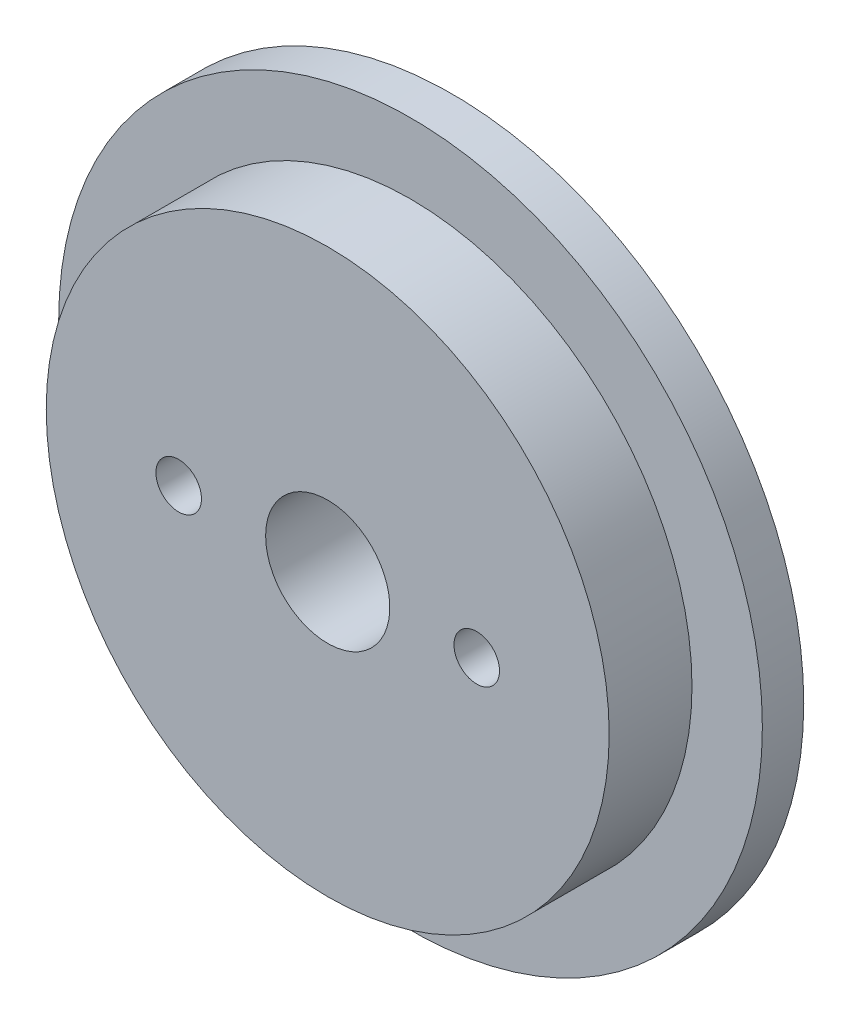
SolidWorks part; units mm, degrees
ref_plane "Ebene vorne" through (0, 0, 0) normal (0, 0, 1) x (1, 0, 0)
ref_plane "Ebene oben" through (0, 0, 0) normal (0, 1, 0) x (1, 0, 0)
ref_plane "Ebene rechts" through (0, 0, 0) normal (1, 0, 0) x (0, 0, -1)
sketch "Skizze1" plane through (0, 0, 0) normal (0, 0, 1) x (1, 0, 0)
  circle A0 centre (0, 0) radius 34
  dimension "D1" = 68
extrude "Aufsatz-Linear austragen1" add sketch "Skizze1" along normal blind 10 contours A0
sketch "Skizze3" plane through (0, 0, 0) normal (0, 0, -1) x (-1, 0, 0)
  circle A0 centre (0, 0) radius 42.5
  dimension "D1" = 85
extrude "Aufsatz-Linear austragen2" add sketch "Skizze3" along normal blind 5
hole_wizard "Ø15.0 (15) Durchmesser Bohrung1" positions "Skizze4" profile "Skizze5" hole size "Ø15.0" standard "ISO" end condition through all
sketch "Skizze4" plane through (0, 0, -5) normal (0, 0, -1) x (-1, 0, 0)
  point P0 (0, 0)
sketch "Skizze5" plane through (0, 0, -5) normal (1, 0, 0) x (0, 1, 0)
  line L0 (0, 0) -> (0, 15)
  line L1 (0, 15) -> (7.5, 15)
  line L2 (7.5, 15) -> (7.5, 0)
  line L5 (7.5, 0) -> (0, 0)
  line L11 (0, -6.35) -> (0, 107.95) construction
  dimension "Bohrerdurchmesser" = 15
  dimension "Bohrungstiefe" = 15
hole_wizard "Ø5.5 (5.5) Durchmesser Bohrung1" positions "Skizze7" profile "Skizze8" hole size "Ø5.5" standard "ISO" end condition through all
sketch "Skizze7" plane through (0, 0, -5) normal (0, 0, -1) x (-1, 0, 0)
  point P0 (18, 0)
  point P2 (-18, 0)
  dimension "D1" = 18
  dimension "D2" = 18
sketch "Skizze8" plane through (-18, 0, -5) normal (1, 0, 0) x (0, 1, 0)
  line L0 (0, 0) -> (0, 15)
  line L1 (0, 15) -> (2.75, 15)
  line L2 (2.75, 15) -> (2.75, 0)
  line L5 (2.75, 0) -> (0, 0)
  line L11 (0, -6.35) -> (0, 107.95) construction
  dimension "Bohrerdurchmesser" = 5.5
  dimension "Bohrungstiefe" = 15
